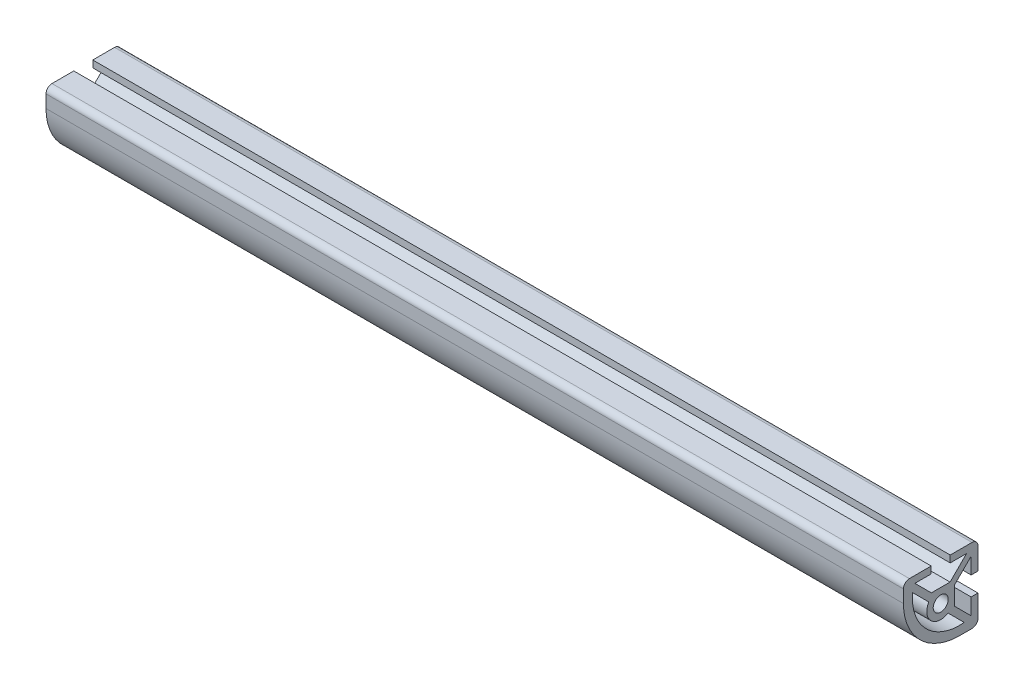
SolidWorks part; units mm, degrees
ref_plane "Front Plane" through (0, 0, 0) normal (0, 0, 1) x (1, 0, 0)
ref_plane "Top Plane" through (0, 0, 0) normal (0, 1, 0) x (1, 0, 0)
ref_plane "Right Plane" through (0, 0, 0) normal (1, 0, 0) x (0, 0, -1)
sketch "Sketch1" plane through (0, 0, 0) normal (1, 0, 0) x (0, 0, -1)
  line L0 (8.0038, -9.5663) -> (2.4852, -4.0478) construction
  line L1 (-4.0478, 2.4852) -> (-9.5663, 8.0038) construction
  line L2 (-3.1872, 4.7498) -> (-8.8006, 10.3632) construction
  line L3 (-8.8006, 10.3632) -> (-3.2385, 10.3632) construction
  line L4 (-3.2385, 10.3632) -> (-3.2385, 12.7) construction
  line L5 (-3.2385, 12.7) -> (-10.668, 12.7) construction
  line L6 (-12.7, 10.668) -> (-12.7, 6.35) construction
  line L7 (6.35, -12.7) -> (10.668, -12.7) construction
  line L8 (12.7, -10.668) -> (12.7, -3.2385) construction
  line L9 (12.7, -3.2385) -> (10.3632, -3.2385) construction
  line L10 (10.3632, -3.2385) -> (10.3632, -8.8006) construction
  line L11 (10.3632, -8.8006) -> (4.7498, -3.1872) construction
  line L12 (4.7498, -3.1872) -> (4.7498, 3.1872) construction
  line L13 (4.7498, 3.1872) -> (10.3632, 8.8006) construction
  line L14 (10.3632, 8.8006) -> (10.3632, 3.2385) construction
  line L15 (10.3632, 3.2385) -> (12.7, 3.2385) construction
  line L16 (12.7, 3.2385) -> (12.7, 10.668) construction
  line L17 (10.668, 12.7) -> (3.2385, 12.7) construction
  line L18 (3.2385, 12.7) -> (3.2385, 10.3632) construction
  line L19 (3.2385, 10.3632) -> (8.8006, 10.3632) construction
  line L20 (8.8006, 10.3632) -> (3.1872, 4.7498) construction
  line L21 (3.1872, 4.7498) -> (-3.1872, 4.7498) construction
  line L22 (-12.7, 0) -> (12.7, 0) construction
  line L23 (0, -12.7) -> (0, 12.7) construction
  line L24 (-7.1204, -7.1204) -> (-4.9651, -4.9651) construction
  line L25 (11.5316, -3.2385) -> (11.5316, 3.2385) construction
  line L26 (-3.2385, 11.5316) -> (3.2385, 11.5316) construction
  line L27 (11.5316, 0) -> (4.7498, 0) construction
  line L28 (0, 11.5316) -> (0, 4.7498) construction
  line L29 (-9.5663, 8.0038) -> (-8.0038, 9.5663) construction
  line L30 (3.1872, 4.7498) -> (4.7498, 3.1872) construction
  circle A0 centre (0, 0) radius 2.5527 construction
  arc A1 (-10.668, 12.7) -> (-12.7, 10.668) centre (-10.668, 10.668) ccw construction
  arc A2 (-12.7, 6.35) -> (6.35, -12.7) centre (6.35, 6.35) ccw construction
  arc A4 (12.7, 10.668) -> (10.668, 12.7) centre (10.668, 10.668) ccw construction
  arc A5 (-4.0478, 2.4852) -> (2.4852, -4.0478) centre (0, 0) ccw construction
  arc A6 (-9.5663, 8.0038) -> (8.0038, -9.5663) centre (6.35, 6.35) ccw construction
  arc A7 (12.7, -10.668) -> (10.668, -12.7) centre (10.668, -10.668) cw construction
  dimension "Radius" = 19.05
  dimension "Corner Radius" = 2.032
  dimension "Center Diameter" = 5.1054
  dimension "Rail Width" = 25.4
  dimension "Outer Thickness" = 2.3368
  dimension "Radius Thickness" = 3.048
  dimension "Leg Thickness" = 2.2098
  dimension "Rail Height" = 25.4
  dimension "TSlot Width" = 6.477
  dimension "TSlot Depth" = 7.9502
sketch "Sketch2" plane through (0, 0, 0) normal (0, 0, 1) x (1, 0, 0)
  line L0 (-146.05, 0) -> (146.05, 0) construction
  point P2 (-95.25, 0)
  point P4 (95.25, 0)
  dimension "Length" = 292.1
  dimension "D1" = 50.8
  dimension "D2" = 50.8
sketch "Sketch3" plane through (0, 0, 0) normal (1, 0, 0) x (0, 0, -1)
  line L0 (-10.668, 12.7) -> (-3.2385, 12.7)
  line L1 (-3.2385, 12.7) -> (-3.2385, 10.3632)
  line L2 (-3.2385, 10.3632) -> (-8.8006, 10.3632)
  line L3 (-8.8006, 10.3632) -> (-3.1872, 4.7498)
  line L4 (-3.1872, 4.7498) -> (3.1872, 4.7498)
  line L5 (3.1872, 4.7498) -> (8.8006, 10.3632)
  line L6 (8.8006, 10.3632) -> (3.2385, 10.3632)
  line L7 (3.2385, 10.3632) -> (3.2385, 12.7)
  line L8 (3.2385, 12.7) -> (10.668, 12.7)
  line L9 (12.7, 10.668) -> (12.7, 3.2385)
  line L10 (12.7, 3.2385) -> (10.3632, 3.2385)
  line L11 (10.3632, 3.2385) -> (10.3632, 8.8006)
  line L12 (10.3632, 8.8006) -> (4.7498, 3.1872)
  line L13 (4.7498, 3.1872) -> (4.7498, -3.1872)
  line L14 (4.7498, -3.1872) -> (10.3632, -8.8006)
  line L15 (10.3632, -8.8006) -> (10.3632, -3.2385)
  line L16 (10.3632, -3.2385) -> (12.7, -3.2385)
  line L17 (12.7, -3.2385) -> (12.7, -10.668)
  line L18 (2.4852, -4.0478) -> (8.0038, -9.5663)
  line L19 (10.668, -12.7) -> (6.35, -12.7)
  line L20 (-9.5663, 8.0038) -> (-4.0478, 2.4852)
  line L21 (-12.7, 10.668) -> (-12.7, 6.35)
  arc A0 (-12.7, 10.668) -> (-10.668, 12.7) centre (-10.668, 10.668) cw
  arc A1 (10.668, 12.7) -> (12.7, 10.668) centre (10.668, 10.668) cw
  arc A2 (12.7, -10.668) -> (10.668, -12.7) centre (10.668, -10.668) cw
  arc A3 (-12.7, 6.35) -> (6.35, -12.7) centre (6.35, 6.35) ccw
  arc A4 (-4.0478, 2.4852) -> (2.4852, -4.0478) centre (0, 0) ccw
  arc A7 (-4.0478, 2.4852) -> (2.4852, -4.0478) centre (0, 0) ccw construction
  arc A8 (-9.5663, 8.0038) -> (8.0038, -9.5663) centre (6.35, 6.35) ccw
  circle A9 centre (0, 0) radius 2.5527
  circle A10 centre (0, 0) radius 2.5527 construction
extrude "Boss-Extrude1" add sketch "Sketch3" along normal up to vertex (146.05 mm away) and the other way up to vertex (146.05 mm away) up to point (146.05, 0, 0) other way up to point (-146.05, 0, 0)
equation "\"D1@Sketch2\"=\"Rail Width@Sketch1\"*2"
equation "\"D2@Sketch2\"=\"D1@Sketch2\""
